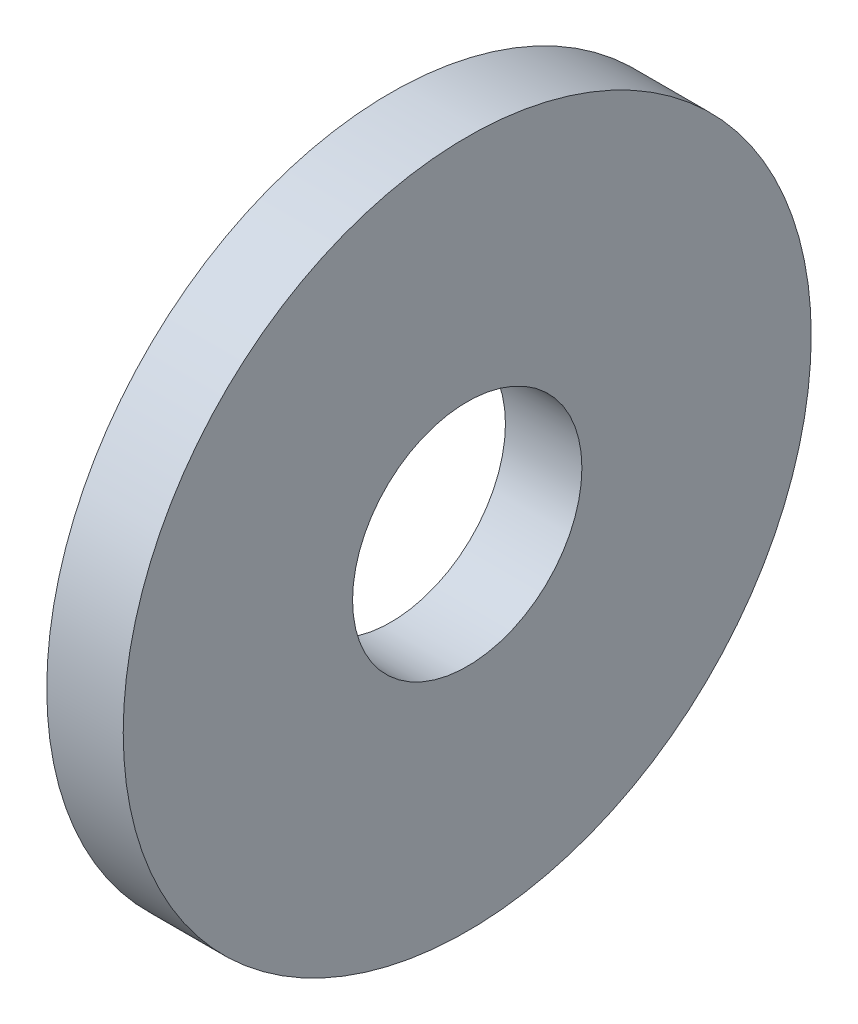
SolidWorks part; units mm, degrees
material "Pine"
ref_plane "Front Plane" through (0, 0, 0) normal (0, 0, 1) x (1, 0, 0)
ref_plane "Top Plane" through (0, 0, 0) normal (0, 1, 0) x (1, 0, 0)
ref_plane "Right Plane" through (0, 0, 0) normal (1, 0, 0) x (0, 0, -1)
sketch "Sketch1" plane through (0, 0, 0) normal (1, 0, 0) x (0, 0, -1)
  circle A0 centre (0, 0) radius 9
  dimension "D1" = 18
extrude "Boss-Extrude1" add sketch "Sketch1" along normal blind 2
sketch "Sketch2" plane through (2, 0, 0) normal (1, 0, 0) x (0, 0, -1)
  circle A2 centre (0, 0) radius 3
extrude "Cut-Extrude1" cut sketch "Sketch2" against normal through all
